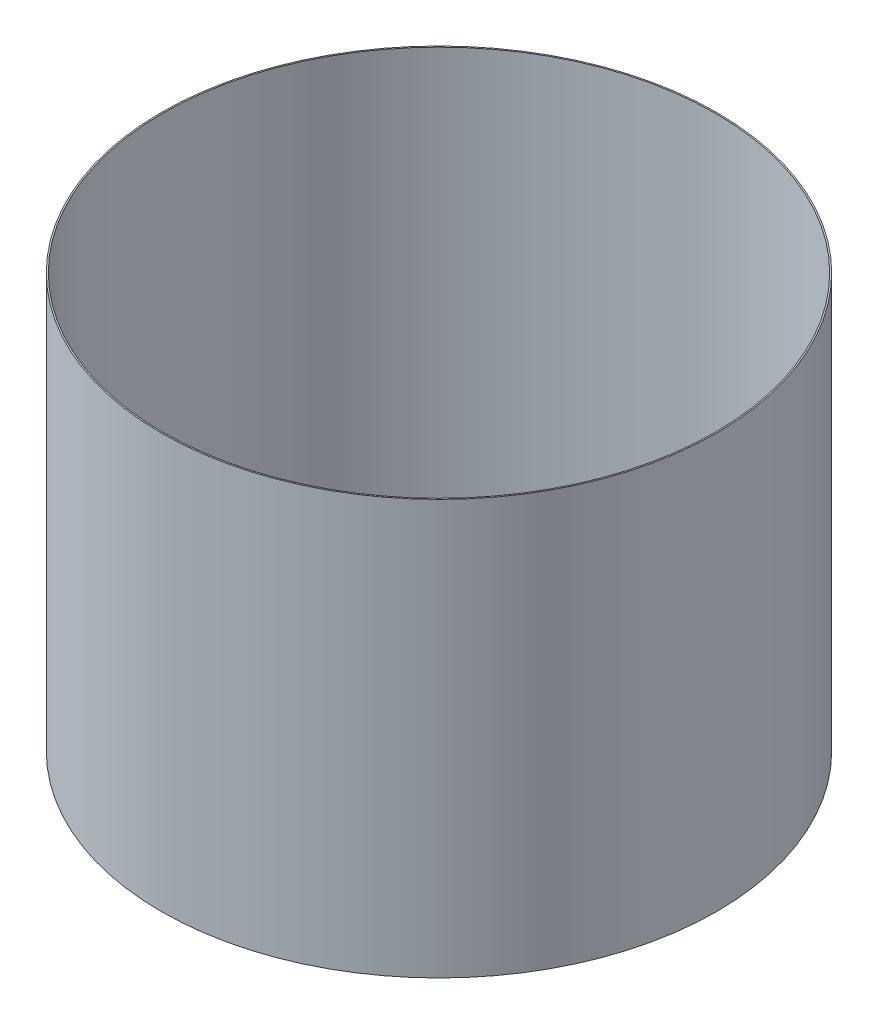
SolidWorks part; units mm, degrees
ref_plane "Front Plane" through (0, 0, 0) normal (0, 0, 1) x (1, 0, 0)
ref_plane "Top Plane" through (0, 0, 0) normal (0, 1, 0) x (1, 0, 0)
ref_plane "Right Plane" through (0, 0, 0) normal (1, 0, 0) x (0, 0, -1)
sketch "Sketch1" plane through (0, 0, 0) normal (0, 1, 0) x (1, 0, 0)
  circle A0 centre (0, 0) radius 2000
  circle A1 centre (0, 0) radius 2010
  dimension "D1" = 4000
  dimension "D2" = 10
extrude "Extrude1" add sketch "Sketch1" along normal blind 3000
